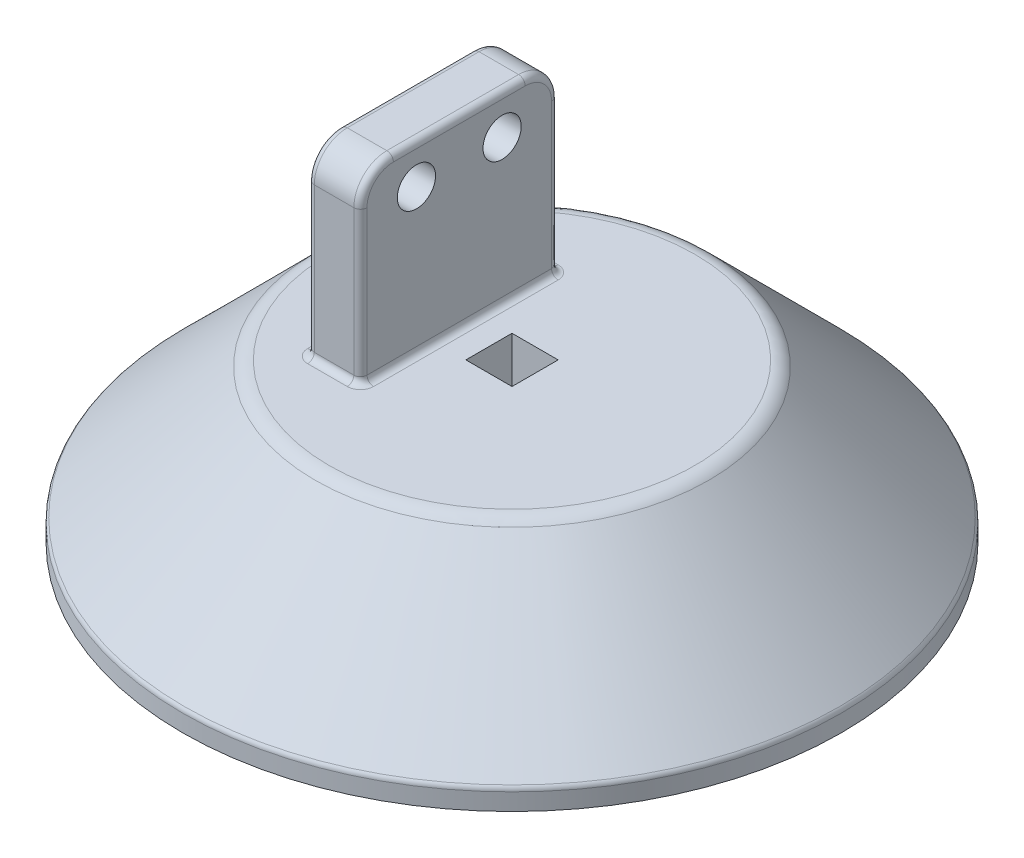
SolidWorks part; units mm, degrees
ref_plane "Front Plane" through (0, 0, 0) normal (0, 0, 1) x (1, 0, 0)
ref_plane "Top Plane" through (0, 0, 0) normal (0, 1, 0) x (1, 0, 0)
ref_plane "Right Plane" through (0, 0, 0) normal (1, 0, 0) x (0, 0, -1)
sketch "Sketch1" plane through (0, 0, 0) normal (0, 0, 1) x (1, 0, 0)
  line L0 (0, 0) -> (0, 24)
  line L1 (0, 24) -> (-29, 24)
  line L2 (-29, 24) -> (-50, 3)
  line L4 (-50, 3) -> (-50, 0)
  line L5 (-50, 0) -> (0, 0)
  dimension "D1" = 3
  dimension "D2" = 50
  dimension "D3" = 21
  dimension "D4" = 29
revolve "Revolve1" add sketch "Sketch1" angle 360 about L0
sketch "Sketch2" plane through (0, 24, 0) normal (0, 1, 0) x (1, 0, 0)
  line L0 (-16, 0) -> (0, 0) construction
  line L2 (-16, 15) -> (-8, 15)
  line L3 (-16, 15) -> (-16, -15)
  line L4 (-16, -15) -> (-8, -15)
  line L5 (-8, 15) -> (-8, -15)
  dimension "D1" = 30
  dimension "D2" = 8
  dimension "D3" = 13
extrude "Boss-Extrude1" add sketch "Sketch2" along normal blind 28
sketch "Sketch3" plane through (0, 0, 0) normal (1, 0, 0) x (0, 0, -1)
  line L0 (-38.3837, 24) -> (38.3837, 24) construction
  line L1 (0, 0) -> (0, 52) construction
  line L2 (-15, 52) -> (15, 52) construction
  line L3 (-6.5, 46) -> (6.5, 46) construction
  circle A0 centre (-6.5, 46) radius 2.9
  circle A1 centre (6.5, 46) radius 2.9
  dimension "D2" = 5.8
  dimension "D1" = 13
  dimension "D3" = 22
extrude "Cut-Extrude1" cut sketch "Sketch3" against normal up to next
fillet "Fillet1" radius 5 2 edges at (-12, 52, -15) (-12, 52, 15)
fillet "Fillet2" radius 3 1 edges at (0, 24, -29)
fillet "Fillet3" radius 1 1 edges at (0, 3, -50)
fillet "Fillet4" radius 1 14 edges at (-16, 35.5, -15) (-16, 50.5355, -13.5355) (-16, 35.5, 15) (-16, 50.5355, 13.5355) (-8, 35.5, 15) (-8, 50.5355, 13.5355) (-8, 35.5, -15) (-8, 50.5355, -13.5355) (-16, 52, 0) (-8, 52, 0) (-12, 24, 15) (-8, 24, 0) (-12, 24, -15) (-16, 24, 0)
sketch "Sketch4" plane through (0, 24, 0) normal (0, 1, 0) x (1, 0, 0)
  line L0 (-3.5, 3.5) -> (3.5, -3.5) construction
  line L1 (-3.5, 3.5) -> (3.5, 3.5)
  line L2 (-3.5, 3.5) -> (-3.5, -3.5)
  line L3 (-3.5, -3.5) -> (3.5, -3.5)
  line L4 (3.5, 3.5) -> (3.5, -3.5)
  dimension "D1" = 7
extrude "Cut-Extrude2" cut sketch "Sketch4" against normal blind 20
